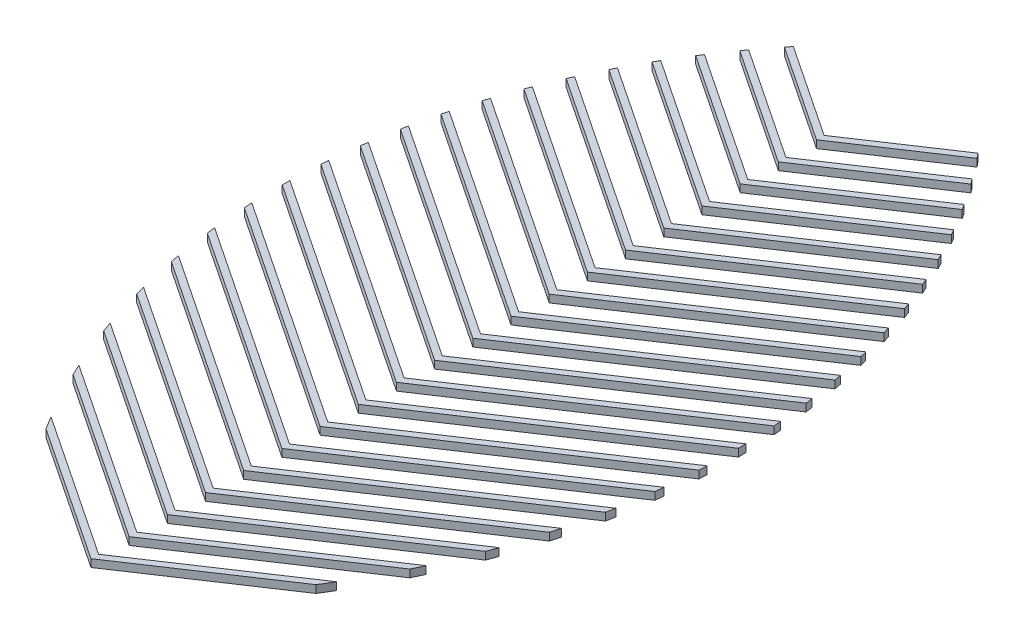
SolidWorks part; units mm, degrees
ref_plane "Front Plane" through (0, 0, 0) normal (0, 0, 1) x (1, 0, 0)
ref_plane "Top Plane" through (0, 0, 0) normal (0, 1, 0) x (1, 0, 0)
ref_plane "Right Plane" through (0, 0, 0) normal (1, 0, 0) x (0, 0, -1)
sketch "Sketch2" plane through (0, 0, 0) normal (0, 1, 0) x (1, 0, 0)
  line L0 (-15.0876, 6.8922) -> (8.6636, -8.942)
  line L1 (8.6636, -8.942) -> (32.4148, 6.8922)
  line L2 (-20.2008, 16.651) -> (8.6636, -2.592)
  line L3 (8.6636, -3.862) -> (8.6636, -8.942) construction
  line L4 (-13.7712, 4.7445) -> (8.6636, -10.212)
  line L5 (8.6636, -10.212) -> (31.0984, 4.7445)
  line L7 (8.6636, -8.942) -> (8.6636, -10.212) construction
  line L9 (8.6636, -2.592) -> (37.5281, 16.651)
  line L10 (-19.336, 14.8045) -> (8.6636, -3.862)
  line L11 (8.6636, -3.862) -> (36.6632, 14.8045)
  line L14 (8.6636, 2.488) -> (8.6636, -2.592) construction
  line L15 (8.6636, -2.592) -> (8.6636, -3.862) construction
  line L16 (-23.6775, 25.3188) -> (8.6636, 3.758)
  line L17 (8.6636, 3.758) -> (41.0047, 25.3188)
  line L18 (-23.0802, 23.6506) -> (8.6636, 2.488)
  line L19 (8.6636, 2.488) -> (40.4074, 23.6506)
  line L22 (8.6636, 8.838) -> (8.6636, 3.758) construction
  line L23 (8.6636, 3.758) -> (8.6636, 2.488) construction
  line L24 (-26.0837, 33.2729) -> (8.6636, 10.108)
  line L25 (8.6636, 10.108) -> (43.4109, 33.2729)
  line L26 (-25.6722, 31.7286) -> (8.6636, 8.838)
  line L27 (8.6636, 8.838) -> (42.9994, 31.7286)
  line L30 (8.6636, 15.188) -> (8.6636, 10.108) construction
  line L31 (8.6636, 10.108) -> (8.6636, 8.838) construction
  line L32 (-27.7036, 40.7028) -> (8.6636, 16.458)
  line L33 (8.6636, 16.458) -> (45.0308, 40.7028)
  line L34 (-27.4334, 39.2527) -> (8.6636, 15.188)
  line L35 (8.6636, 15.188) -> (44.7606, 39.2527)
  line L38 (8.6636, 21.538) -> (8.6636, 16.458) construction
  line L39 (8.6636, 16.458) -> (8.6636, 15.188) construction
  line L40 (-28.7043, 47.72) -> (8.6636, 22.808)
  line L41 (8.6636, 22.808) -> (46.0315, 47.72)
  line L42 (-28.5479, 46.3457) -> (8.6636, 21.538)
  line L43 (8.6636, 21.538) -> (45.8752, 46.3457)
  line L46 (8.6636, 27.888) -> (8.6636, 22.808) construction
  line L47 (8.6636, 22.808) -> (8.6636, 21.538) construction
  line L48 (-29.1937, 54.3963) -> (8.6636, 29.158)
  line L49 (8.6636, 29.158) -> (46.5209, 54.3963)
  line L50 (-29.1328, 53.0857) -> (8.6636, 27.888)
  line L51 (8.6636, 27.888) -> (46.4601, 53.0857)
  line L54 (8.6636, 34.238) -> (8.6636, 29.158) construction
  line L55 (8.6636, 29.158) -> (8.6636, 27.888) construction
  line L56 (-29.246, 60.7811) -> (8.6636, 35.508)
  line L57 (8.6636, 35.508) -> (46.5732, 60.7811)
  line L58 (-29.2677, 59.5256) -> (8.6636, 34.238)
  line L59 (8.6636, 34.238) -> (46.5949, 59.5256)
  line L62 (8.6636, 40.588) -> (8.6636, 35.508) construction
  line L63 (8.6636, 35.508) -> (8.6636, 34.238) construction
  line L64 (-28.9145, 66.9101) -> (8.6636, 41.858)
  line L65 (8.6636, 41.858) -> (46.2417, 66.9101)
  line L66 (-29.0094, 65.7034) -> (8.6636, 40.588)
  line L67 (8.6636, 40.588) -> (46.3367, 65.7034)
  line L70 (8.6636, 46.938) -> (8.6636, 41.858) construction
  line L71 (8.6636, 41.858) -> (8.6636, 40.588) construction
  line L72 (-28.2388, 72.8096) -> (8.6636, 48.208)
  line L73 (8.6636, 48.208) -> (45.566, 72.8096)
  line L74 (-28.3999, 71.647) -> (8.6636, 46.938)
  line L75 (8.6636, 46.938) -> (45.7271, 71.647)
  line L78 (8.6636, 53.288) -> (8.6636, 48.208) construction
  line L79 (8.6636, 48.208) -> (8.6636, 46.938) construction
  line L80 (-27.2489, 78.4997) -> (8.6636, 54.558)
  line L81 (8.6636, 54.558) -> (44.5761, 78.4997)
  line L82 (-27.4708, 77.3777) -> (8.6636, 53.288)
  line L83 (8.6636, 53.288) -> (44.798, 77.3777)
  line L86 (8.6636, 59.638) -> (8.6636, 54.558) construction
  line L87 (8.6636, 54.558) -> (8.6636, 53.288) construction
  line L88 (-25.968, 83.9958) -> (8.6636, 60.908)
  line L89 (8.6636, 60.908) -> (43.2952, 83.9958)
  line L90 (-26.2465, 82.9115) -> (8.6636, 59.638)
  line L91 (8.6636, 59.638) -> (43.5737, 82.9115)
  line L94 (8.6636, 65.988) -> (8.6636, 60.908) construction
  line L95 (8.6636, 60.908) -> (8.6636, 59.638) construction
  line L96 (-24.4139, 89.3097) -> (8.6636, 67.258)
  line L97 (8.6636, 67.258) -> (41.7411, 89.3097)
  line L98 (-24.7458, 88.261) -> (8.6636, 65.988)
  line L99 (8.6636, 65.988) -> (42.073, 88.261)
  line L102 (8.6636, 72.338) -> (8.6636, 67.258) construction
  line L103 (8.6636, 67.258) -> (8.6636, 65.988) construction
  line L104 (-22.6004, 94.4507) -> (8.6636, 73.608)
  line L105 (8.6636, 73.608) -> (39.9276, 94.4507)
  line L106 (-22.9833, 93.436) -> (8.6636, 72.338)
  line L107 (8.6636, 72.338) -> (40.3105, 93.436)
  line L110 (8.6636, 78.688) -> (8.6636, 73.608) construction
  line L111 (8.6636, 73.608) -> (8.6636, 72.338) construction
  line L112 (-20.5381, 99.4258) -> (8.6636, 79.958)
  line L113 (8.6636, 79.958) -> (37.8653, 99.4258)
  line L114 (-20.9701, 98.4438) -> (8.6636, 78.688)
  line L115 (8.6636, 78.688) -> (38.2973, 98.4438)
  line L118 (8.6636, 85.038) -> (8.6636, 79.958) construction
  line L119 (8.6636, 79.958) -> (8.6636, 78.688) construction
  line L120 (-18.2347, 104.2403) -> (8.6636, 86.308)
  line L121 (8.6636, 86.308) -> (35.562, 104.2403)
  line L122 (-18.7144, 103.29) -> (8.6636, 85.038)
  line L123 (8.6636, 85.038) -> (36.0416, 103.29)
  line L126 (8.6636, 91.388) -> (8.6636, 86.308) construction
  line L127 (8.6636, 86.308) -> (8.6636, 85.038) construction
  line L128 (-15.6958, 108.8976) -> (8.6636, 92.658)
  line L129 (8.6636, 92.658) -> (33.023, 108.8976)
  line L130 (-16.2222, 107.9786) -> (8.6636, 91.388)
  line L131 (8.6636, 91.388) -> (33.5494, 107.9786)
  line L134 (8.6636, 97.738) -> (8.6636, 92.658) construction
  line L135 (8.6636, 92.658) -> (8.6636, 91.388) construction
  line L136 (-12.9245, 113.4001) -> (8.6636, 99.008)
  line L137 (8.6636, 99.008) -> (30.2517, 113.4001)
  line L138 (-13.4973, 112.512) -> (8.6636, 97.738)
  line L139 (8.6636, 97.738) -> (30.8245, 112.512)
  line L142 (8.6636, 104.088) -> (8.6636, 99.008) construction
  line L143 (8.6636, 99.008) -> (8.6636, 97.738) construction
  line L144 (-9.9223, 117.7486) -> (8.6636, 105.358)
  line L145 (8.6636, 105.358) -> (27.2495, 117.7486)
  line L146 (-10.5412, 116.8912) -> (8.6636, 104.088)
  line L147 (8.6636, 104.088) -> (27.8684, 116.8912)
  line L150 (8.6636, 110.438) -> (8.6636, 105.358) construction
  line L151 (8.6636, 105.358) -> (8.6636, 104.088) construction
  line L152 (-6.6885, 121.9428) -> (8.6636, 111.708)
  line L153 (8.6636, 111.708) -> (24.0157, 121.9428)
  line L154 (-7.3538, 121.1163) -> (8.6636, 110.438)
  line L155 (8.6636, 110.438) -> (24.6811, 121.1163)
  line L158 (8.6636, 116.788) -> (8.6636, 111.708) construction
  line L159 (8.6636, 111.708) -> (8.6636, 110.438) construction
  arc A0 (-6.6885, 121.9428) -> (-7.3538, 121.1163) centre (71.3713, 58.4122) ccw
  arc A1 (24.0157, 121.9428) -> (24.6811, 121.1163) centre (-54.0441, 58.4122) cw
  arc A2 (32.4148, 6.8922) -> (31.0984, 4.7445) centre (-54.0441, 58.4122) cw
  arc A3 (37.5281, 16.651) -> (36.6632, 14.8045) centre (-54.0441, 58.4122) cw
  arc A4 (41.0047, 25.3188) -> (40.4074, 23.6506) centre (-54.0441, 58.4122) cw
  arc A5 (43.4109, 33.2729) -> (42.9994, 31.7286) centre (-54.0441, 58.4122) cw
  arc A6 (45.0308, 40.7028) -> (44.7606, 39.2527) centre (-54.0441, 58.4122) cw
  arc A7 (46.0315, 47.72) -> (45.8752, 46.3457) centre (-54.0441, 58.4122) cw
  arc A8 (46.5209, 54.3963) -> (46.4601, 53.0857) centre (-54.0441, 58.4122) cw
  arc A9 (46.5732, 60.7811) -> (46.5949, 59.5256) centre (-54.0441, 58.4122) cw
  arc A10 (46.2417, 66.9101) -> (46.3367, 65.7034) centre (-54.0441, 58.4122) cw
  arc A11 (45.566, 72.8096) -> (45.7271, 71.647) centre (-54.0441, 58.4122) cw
  arc A12 (44.5761, 78.4997) -> (44.798, 77.3777) centre (-54.0441, 58.4122) cw
  arc A13 (43.2952, 83.9958) -> (43.5737, 82.9115) centre (-54.0441, 58.4122) cw
  arc A14 (41.7411, 89.3097) -> (42.073, 88.261) centre (-54.0441, 58.4122) cw
  arc A15 (39.9276, 94.4507) -> (40.3105, 93.436) centre (-54.0441, 58.4122) cw
  arc A16 (37.8653, 99.4258) -> (38.2973, 98.4438) centre (-54.0441, 58.4122) cw
  arc A17 (35.562, 104.2403) -> (36.0416, 103.29) centre (-54.0441, 58.4122) cw
  arc A18 (33.023, 108.8976) -> (33.5494, 107.9786) centre (-54.0441, 58.4122) cw
  arc A19 (30.2517, 113.4001) -> (30.8245, 112.512) centre (-54.0441, 58.4122) cw
  arc A20 (27.2495, 117.7486) -> (27.8684, 116.8912) centre (-54.0441, 58.4122) cw
  arc A21 (-15.0876, 6.8922) -> (-13.7712, 4.7445) centre (71.3713, 58.4122) ccw
  arc A22 (-23.6775, 25.3188) -> (-23.0802, 23.6506) centre (71.3713, 58.4122) ccw
  arc A23 (-20.2008, 16.651) -> (-19.336, 14.8045) centre (71.3713, 58.4122) ccw
  arc A24 (-26.0837, 33.2729) -> (-25.6722, 31.7286) centre (71.3713, 58.4122) ccw
  arc A25 (-27.7036, 40.7028) -> (-27.4334, 39.2527) centre (71.3713, 58.4122) ccw
  arc A26 (-28.7043, 47.72) -> (-28.5479, 46.3457) centre (71.3713, 58.4122) ccw
  arc A27 (-29.1937, 54.3963) -> (-29.1328, 53.0857) centre (71.3713, 58.4122) ccw
  arc A28 (-29.246, 60.7811) -> (-29.2677, 59.5256) centre (71.3713, 58.4122) ccw
  arc A29 (-28.9145, 66.9101) -> (-29.0094, 65.7034) centre (71.3713, 58.4122) ccw
  arc A30 (-28.2388, 72.8096) -> (-28.3999, 71.647) centre (71.3713, 58.4122) ccw
  arc A31 (-27.2489, 78.4997) -> (-27.4708, 77.3777) centre (71.3713, 58.4122) ccw
  arc A32 (-25.968, 83.9958) -> (-26.2465, 82.9115) centre (71.3713, 58.4122) ccw
  arc A33 (-24.4139, 89.3097) -> (-24.7458, 88.261) centre (71.3713, 58.4122) ccw
  arc A34 (-22.6004, 94.4507) -> (-22.9833, 93.436) centre (71.3713, 58.4122) ccw
  arc A35 (-20.5381, 99.4258) -> (-20.9701, 98.4438) centre (71.3713, 58.4122) ccw
  arc A36 (-18.2347, 104.2403) -> (-18.7144, 103.29) centre (71.3713, 58.4122) ccw
  arc A37 (-15.6958, 108.8976) -> (-16.2222, 107.9786) centre (71.3713, 58.4122) ccw
  arc A38 (-12.9245, 113.4001) -> (-13.4973, 112.512) centre (71.3713, 58.4122) ccw
  arc A39 (-9.9223, 117.7486) -> (-10.5412, 116.8912) centre (71.3713, 58.4122) ccw
  dimension "D1" = 1.27
  dimension "D3" = 20
extrude "Boss-Extrude1" add sketch "Sketch2" along normal blind 1.27
